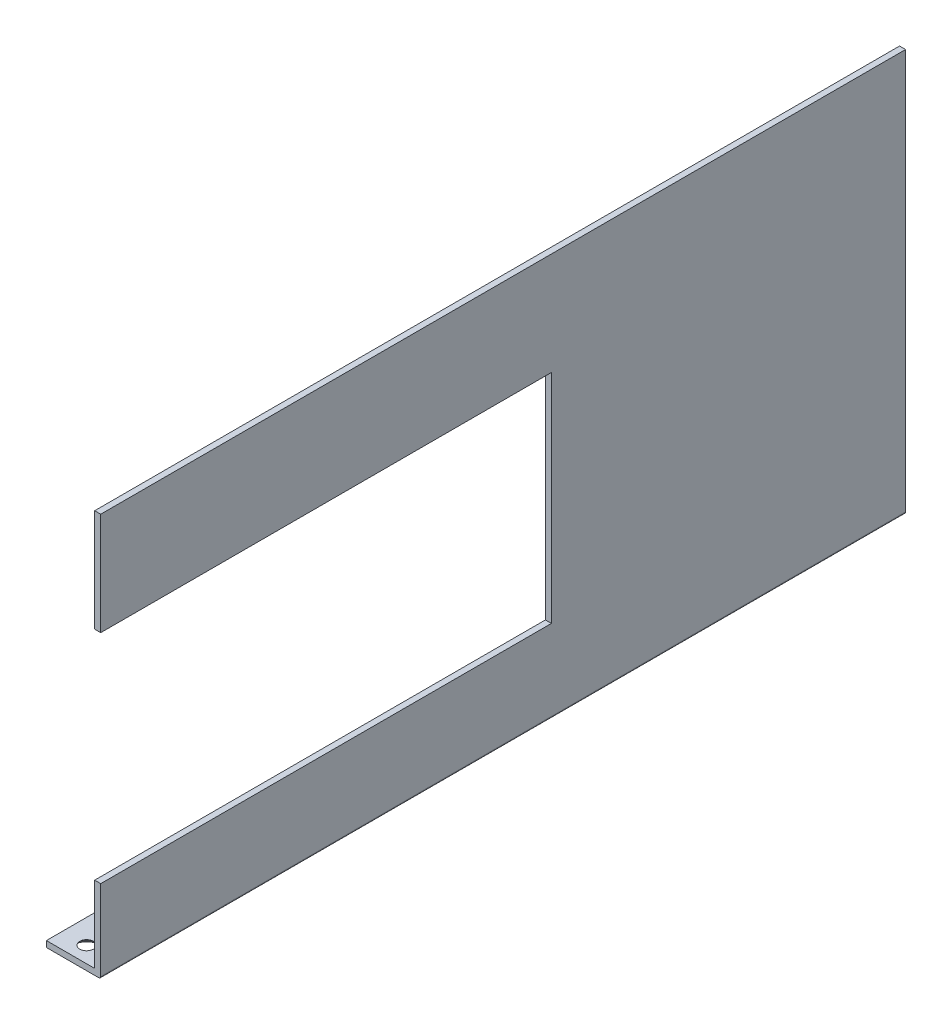
SolidWorks part; units mm, degrees
ref_plane "Front Plane" through (0, 0, 0) normal (0, 0, 1) x (1, 0, 0)
ref_plane "Top Plane" through (0, 0, 0) normal (0, 1, 0) x (1, 0, 0)
ref_plane "Right Plane" through (0, 0, 0) normal (1, 0, 0) x (0, 0, -1)
sketch "Sketch1" plane through (0, 0, 0) normal (0, 0, 1) x (1, 0, 0)
  line L0 (0, 0) -> (13.5, 0)
  line L1 (13.5, 0) -> (13.5, 100)
  line L2 (13.5, 100) -> (12, 100)
  line L3 (12, 100) -> (12, 1.5)
  line L4 (12, 1.5) -> (0, 1.5)
  line L5 (0, 1.5) -> (0, 0)
extrude "Extrude1" add sketch "Sketch1" along normal blind 200
sketch "Sketch2" plane through (0, 0, 0) normal (0, 0, 1) x (1, 0, 0)
  line L0 (12, 1.5) -> (12, 20.5) construction
  line L1 (12, 100) -> (12, 1.5) construction
  line L2 (12, 20.5) -> (13.5, 20.5)
  line L3 (13.5, 0) -> (13.5, 100) construction
  line L4 (13.5, 20.5) -> (13.5, 74.5)
  line L5 (13.5, 74.5) -> (12, 74.5)
  line L6 (12, 74.5) -> (12, 20.5)
fillet "Fillet1" radius 0.5 1 edges at (13.5, 0, 100)
extrude "Cut-Extrude2" cut sketch "Sketch2" against normal blind 112 from surface at 200 starting at face at (9.1577, 29.0566, 200)
sketch "Sketch3" plane through (0, 0, 0) normal (0, -1, 0) x (1, 0, 0)
  line L0 (6, 200) -> (6, 0) construction
  line L1 (0, 200) -> (13, 200) construction
  line L2 (0, 0) -> (13, 0) construction
  point P6 (6, 196)
  point P7 (6, 4)
hole_wizard "CSK for M3 Countersunk Flat Head Screw1" positions "3DSketch1" profile "Sketch5" countersink size "M3" standard "DIN"
sketch3d "3DSketch1"
  point P0 (6, 0, 196)
  point P3 (6, 0, 4)
sketch "Sketch5" plane through (6, 0, 196) normal (1, 0, 0) x (0, 0, -1)
  line L0 (0, 0) -> (0, 2.5215)
  line L1 (0, 2.5215) -> (1.7, 1.5)
  line L2 (1.7, 1.5) -> (1.7, 1.45)
  line L3 (1.7, 1.45) -> (3.15, 0)
  line L5 (3.15, 0) -> (0, 0)
  line L6 (-1.7, 1.45) -> (-3.15, 0) construction
  line L10 (0, 2.5215) -> (-1.7, 1.5) construction
  line L11 (0, -6.35) -> (0, 107.95) construction
  dimension "Hole Dia." = 3.4
  dimension "Hole Depth" = 1.5
  dimension "Near C'Sink Dia." = 6.3
  dimension "Near C'Sink Angle" = 90
  dimension "Drill Angle" = 118
